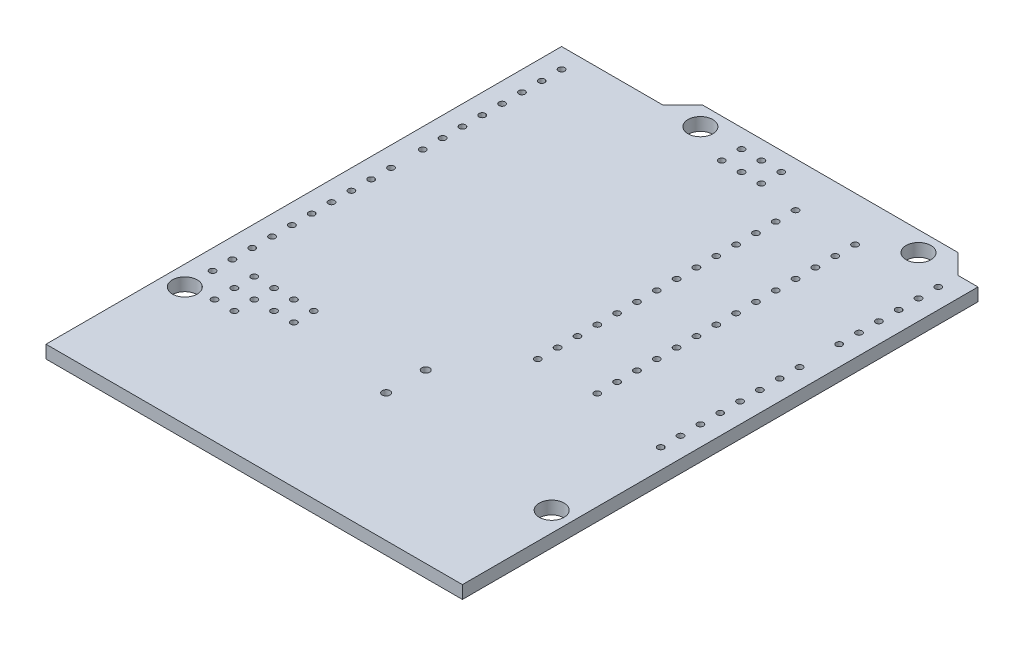
SolidWorks part; units mm, degrees
material "E-Glass Fiber"
ref_plane "Front Plane" through (0, 0, 0) normal (0, 0, 1) x (1, 0, 0)
ref_plane "Top Plane" through (0, 0, 0) normal (0, 1, 0) x (1, 0, 0)
ref_plane "Right Plane" through (0, 0, 0) normal (1, 0, 0) x (0, 0, -1)
sketch "Sketch1" plane through (0, 0, 0) normal (0, 1, 0) x (1, 0, 0)
  line L0 (-29.337, 0) -> (29.337, 0) construction
  line L1 (0, 0) -> (-53.34, 0)
  line L2 (0, 0) -> (0, 66.04)
  line L3 (-5.08, 68.58) -> (-37.846, 68.58)
  line L4 (-53.34, 0) -> (-53.34, 66.04)
  line L5 (-53.34, 66.04) -> (-40.386, 66.04)
  line L6 (-40.386, 66.04) -> (-37.846, 68.58)
  line L7 (-5.08, 68.58) -> (-2.54, 66.04)
  line L8 (-2.54, 66.04) -> (0, 66.04)
  circle A0 centre (-7.62, 66.04) radius 1.5875
  circle A1 centre (-35.56, 66.04) radius 1.5875
  circle A2 centre (-2.54, 13.97) radius 1.5875
  circle A3 centre (-50.8, 15.24) radius 1.5875
  dimension "D8" = 3.175
  dimension "D1" = 68.58
  dimension "D2" = 53.34
  dimension "D3" = 66.04
  dimension "D4" = 2.54
  dimension "D5" = 45
  dimension "D6" = 45
  dimension "D7" = 40.386
  dimension "D9" = 66.04
  dimension "D10" = 35.56
  dimension "D11" = 7.62
  dimension "D12" = 13.97
  dimension "D13" = 2.54
  dimension "D14" = 15.24
  dimension "D15" = 50.8
extrude "Boss-Extrude1" add sketch "Sketch1" against normal blind 1.65
sketch "Sketch2" plane through (0, 0, 0) normal (0, 1, 0) x (1, 0, 0)
  line L0 (0, -0.9075) -> (0, 0.9075) construction
  line L1 (-0.9075, 0) -> (0.9075, 0) construction
  circle A0 centre (-2.54, 27.94) radius 0.4
  dimension "D1" = 0.8
  dimension "D2" = 2.54
  dimension "D3" = 27.94
extrude "Cut-Extrude1" cut sketch "Sketch2" against normal blind 1.65
sketch "Sketch3" plane through (0, 0, 0) normal (0, 1, 0) x (1, 0, 0)
  line L0 (0, -0.9075) -> (0, 0.9075) construction
  line L1 (-0.9075, 0) -> (0.9075, 0) construction
  circle A0 centre (-50.8, 18.796) radius 0.4
  dimension "D2" = 0.8
  dimension "D1" = 50.8
  dimension "D3" = 18.796
extrude "Cut-Extrude2" cut sketch "Sketch3" against normal blind 1.65
pattern_linear "LPattern1" count 15 spacing 2.54 along (0, 0, -1) skipping (8, 0) of "Cut-Extrude1"
sketch "Sketch4" plane through (0, 0, 0) normal (0, 1, 0) x (1, 0, 0)
  line L0 (-0.9075, 0) -> (0.9075, 0) construction
  line L1 (0, -0.9075) -> (0, 0.9075) construction
  circle A0 centre (-50.8, 45.72) radius 0.4
  dimension "D3" = 0.8
  dimension "D1" = 45.72
  dimension "D2" = 50.8
extrude "Cut-Extrude3" cut sketch "Sketch4" against normal blind 1.65
pattern_linear "LPattern2" count 10 spacing 2.54 along (0, 0, -1) of "Cut-Extrude2"
pattern_linear "LPattern3" count 8 spacing 2.54 along (0, 0, -1) of "Cut-Extrude3"
sketch "Sketch5" plane through (0, 0, 0) normal (0, 1, 0) x (1, 0, 0)
  line L0 (-27.89, 66.18) -> (-27.89, 63.64) construction
  line L1 (-30.43, 66.18) -> (-25.35, 66.18) construction
  line L2 (-30.43, 66.18) -> (-30.43, 63.64) construction
  line L3 (-30.43, 63.64) -> (-25.35, 63.64) construction
  line L4 (-25.35, 66.18) -> (-25.35, 63.64) construction
  line L5 (-0.9075, 0) -> (0.9075, 0) construction
  line L6 (0, -0.9075) -> (0, 0.9075) construction
  circle A0 centre (-30.43, 66.18) radius 0.4
  circle A1 centre (-27.89, 66.18) radius 0.4
  circle A2 centre (-25.35, 66.18) radius 0.4
  circle A3 centre (-25.35, 63.64) radius 0.4
  circle A4 centre (-27.89, 63.64) radius 0.4
  circle A5 centre (-30.43, 63.64) radius 0.4
  circle A6 centre (-47.498, 15.748) radius 0.4
  circle A7 centre (-47.498, 18.288) radius 0.4
  circle A8 centre (-47.498, 20.828) radius 0.4
  circle A9 centre (-44.958, 20.828) radius 0.4
  circle A10 centre (-44.958, 18.288) radius 0.4
  circle A11 centre (-44.958, 15.748) radius 0.4
  circle A12 centre (-42.418, 18.288) radius 0.4
  circle A13 centre (-42.418, 20.828) radius 0.4
  circle A14 centre (-39.878, 20.828) radius 0.4
  circle A15 centre (-39.878, 18.288) radius 0.4
  circle A16 centre (-26.162, 21.463) radius 0.5
  circle A17 centre (-26.162, 16.383) radius 0.5
extrude "Cut-Extrude4" cut sketch "Sketch5" against normal blind 10
sketch "Sketch6" plane through (0, 0, 0) normal (0, 1, 0) x (1, 0, 0)
  line L0 (0, -0.9075) -> (0, 0.9075) construction
  line L1 (-0.9075, 0) -> (0.9075, 0) construction
  line L2 (-20.193, 29.845) -> (-20.193, 32.385) construction
  circle A0 centre (-20.193, 29.845) radius 0.4
  circle A1 centre (-12.573, 29.845) radius 0.4
  circle A2 centre (-20.193, 32.385) radius 0.4
  circle A3 centre (-12.573, 32.385) radius 0.4
  circle A4 centre (-20.193, 34.925) radius 0.4
  circle A5 centre (-12.573, 34.925) radius 0.4
  circle A6 centre (-20.193, 37.465) radius 0.4
  circle A7 centre (-12.573, 37.465) radius 0.4
  circle A8 centre (-20.193, 40.005) radius 0.4
  circle A9 centre (-12.573, 40.005) radius 0.4
  circle A10 centre (-20.193, 42.545) radius 0.4
  circle A11 centre (-12.573, 42.545) radius 0.4
  circle A12 centre (-20.193, 45.085) radius 0.4
  circle A13 centre (-12.573, 45.085) radius 0.4
  circle A14 centre (-20.193, 47.625) radius 0.4
  circle A15 centre (-12.573, 47.625) radius 0.4
  circle A16 centre (-20.193, 50.165) radius 0.4
  circle A17 centre (-12.573, 50.165) radius 0.4
  circle A18 centre (-20.193, 52.705) radius 0.4
  circle A19 centre (-12.573, 52.705) radius 0.4
  circle A20 centre (-20.193, 55.245) radius 0.4
  circle A21 centre (-12.573, 55.245) radius 0.4
  circle A22 centre (-20.193, 57.785) radius 0.4
  circle A23 centre (-12.573, 57.785) radius 0.4
  circle A24 centre (-20.193, 60.325) radius 0.4
  circle A25 centre (-12.573, 60.325) radius 0.4
  circle A26 centre (-20.193, 62.865) radius 0.4
  circle A27 centre (-12.573, 62.865) radius 0.4
  dimension "D1" = 0.8
  dimension "D2" = 7.62
  dimension "D3" = 12.573
  dimension "D4" = 29.845
  dimension "D6" = 2.54
  dimension "D5" = 14
extrude "Cut-Extrude5" cut sketch "Sketch6" against normal blind 10
equation "\"D13@Sketch5\"=0.001*25.4*620"
equation "\"D16@Sketch5\"=645*0.001*25.4"
